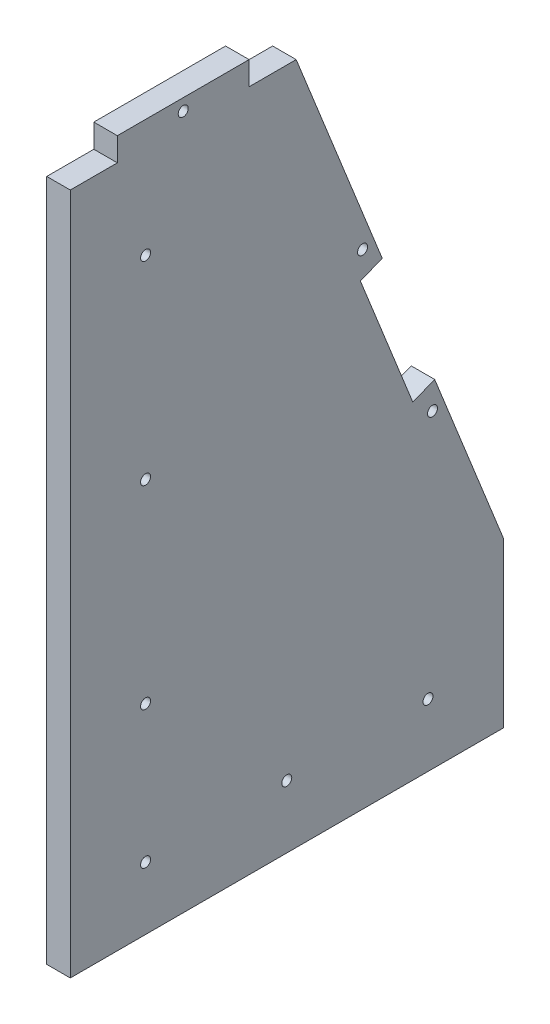
SolidWorks part; units mm, degrees
material "Pine"
ref_plane "Front Plane" through (0, 0, 0) normal (0, 0, 1) x (1, 0, 0)
ref_plane "Top Plane" through (0, 0, 0) normal (0, 1, 0) x (1, 0, 0)
ref_plane "Right Plane" through (0, 0, 0) normal (1, 0, 0) x (0, 0, -1)
sketch "Sketch1" plane through (0, 0, 0) normal (-1, 0, 0) x (0, -1, 0)
  line L0 (-381, 0) -> (-381, -116.84)
  line L1 (-368.3, 0) -> (-368.3, -121.92) construction
  line L2 (-33.8667, -40.64) -> (-36.5667, -40.64) construction
  line L3 (-105.25, -40.64) -> (-320.2, -40.64) construction
  line L4 (-57.15, 0) -> (-57.15, -233.68) construction
  line L10 (-381, -116.84) -> (-88.9, -233.68)
  line L15 (0, -233.68) -> (0, 0)
  line L16 (0, 0) -> (-381, 0)
  line L24 (-33.8667, -40.64) -> (-33.8667, -193.04) construction
  line L25 (0, -233.68) -> (-88.9, -233.68)
  circle A0 centre (-212.725, -40.64) radius 2.7
  circle A1 centre (-317.5, -40.64) radius 2.7
  circle A2 centre (-107.95, -40.64) radius 2.7
  circle A8 centre (-33.8667, -193.04) radius 2.7
  circle A9 centre (-33.8667, -40.64) radius 2.7
  circle A10 centre (-33.8667, -116.84) radius 2.7
  dimension "D3" = 12.7
  dimension "D12" = 57.15
  dimension "D11" = 5.4
  dimension "D15" = 209.55
  dimension "D2" = 40.64
  dimension "D4" = 33.8667
  dimension "D5" = 152.4
  dimension "D6" = 233.68
  dimension "D7" = 88.9
  dimension "D8" = 116.84
  dimension "D9" = 381
  dimension "D10" = 314.6013
  dimension "D13" = 50.8
  dimension "D14" = 50.8
  dimension "D16" = 104.775
extrude "Boss-Extrude1" add sketch "Sketch1" against normal blind 12.7
sketch "Sketch3" plane through (12.7, 0, 0) normal (1, 0, 0) x (0, 0, -1)
  line L0 (0, 381) -> (116.84, 381) construction
  line L1 (0, 381) -> (25.4, 381)
  line L2 (0, 381) -> (0, 368.3)
  line L3 (0, 368.3) -> (25.4, 368.3)
  line L4 (25.4, 381) -> (25.4, 368.3)
  line L5 (96.52, 381) -> (121.92, 381)
  line L6 (96.52, 381) -> (96.52, 368.3)
  line L7 (96.52, 368.3) -> (121.92, 368.3)
  line L8 (121.92, 381) -> (121.92, 368.3)
  line L9 (116.84, 381) -> (233.68, 88.9) construction
  line L10 (25.4, 374.65) -> (96.52, 374.65) construction
  circle A0 centre (60.96, 374.65) radius 2.7
  dimension "D5" = 5.4
  dimension "D1" = 25.4
  dimension "D2" = 12.7
  dimension "D3" = 12.7
  dimension "D4" = 25.4
  dimension "D6" = 35.56
extrude "top hole" cut sketch "Sketch3" against normal up to next
sketch "Sketch4" plane through (12.7, 0, 0) normal (1, 0, 0) x (0, 0, -1)
  line L0 (131.3533, 344.7167) -> (158.9334, 275.7666) construction
  line L1 (147.1417, 271.05) -> (119.5617, 340) construction
  line L2 (233.68, 88.9) -> (221.8883, 84.1833) construction
  line L3 (221.8883, 84.1833) -> (194.3083, 153.1334) construction
  line L4 (119.5617, 340) -> (131.3533, 344.7167) construction
  line L5 (121.92, 368.3) -> (233.68, 88.9) construction
  line L6 (131.3533, 344.7167) -> (158.9334, 275.7666) construction
  line L7 (182.5167, 216.8083) -> (170.725, 212.0917) construction
  line L8 (153.0375, 273.4083) -> (200.2041, 155.4917) construction
  line L9 (147.1417, 271.05) -> (158.9334, 275.7666) construction
  line L10 (156.575, 247.4666) -> (184.875, 176.7167)
  line L11 (194.3083, 153.1334) -> (206.1, 157.8501) construction
  line L12 (196.6666, 181.4334) -> (168.3667, 252.1833)
  line L13 (156.575, 247.4666) -> (168.3667, 252.1833)
  line L14 (184.875, 176.7167) -> (196.6666, 181.4334)
  line L15 (168.3667, 252.1833) -> (196.6666, 181.4334) construction
  line L16 (168.3667, 252.1833) -> (196.6666, 181.4334) construction
  line L17 (184.875, 176.7167) -> (156.575, 247.4666) construction
  line L18 (206.1, 157.8501) -> (233.68, 88.9) construction
  line L19 (206.1, 157.8501) -> (233.68, 88.9) construction
  line L20 (233.68, 88.9) -> (131.3533, 344.7167) construction
  line L21 (121.92, 368.3) -> (233.68, 88.9) construction
  circle A0 centre (157.7542, 261.6166) radius 2.7
  circle A1 centre (195.4875, 167.2834) radius 2.7
  point P10 (176.6208, 214.45)
  dimension "D5" = 5.4
  dimension "D1" = 12.7
  dimension "D2" = 127
  dimension "D3" = 25.4
  dimension "D4" = 25.4
  dimension "D6" = 12.7
  dimension "D7" = 12.7
  dimension "D8" = 25.4
extrude "back holes" cut sketch "Sketch4" against normal up to next
sketch "Sketch5" plane through (12.7, 0, 0) normal (1, 0, 0) x (0, 0, -1)
  line L0 (156.575, 247.4666) -> (184.875, 176.7167) construction
  line L1 (108.7234, 210.4) -> (157.7234, 210.4) construction
  line L2 (108.7234, 210.4) -> (108.7234, 152.4) construction
  line L3 (108.7234, 152.4) -> (157.7234, 152.4) construction
  line L4 (157.7234, 210.4) -> (157.7234, 152.4) construction
  line L5 (233.68, 0) -> (0, 0) construction
  circle A0 centre (157.7234, 210.4) radius 1.625
  circle A1 centre (108.7234, 210.4) radius 1.625
  circle A2 centre (108.7234, 152.4) radius 1.625
  circle A3 centre (157.7234, 152.4) radius 1.625
  dimension "D1" = 49
  dimension "D3" = 3.25
  dimension "D2" = 58
  dimension "D4" = 12.7
  dimension "D5" = 152.4
